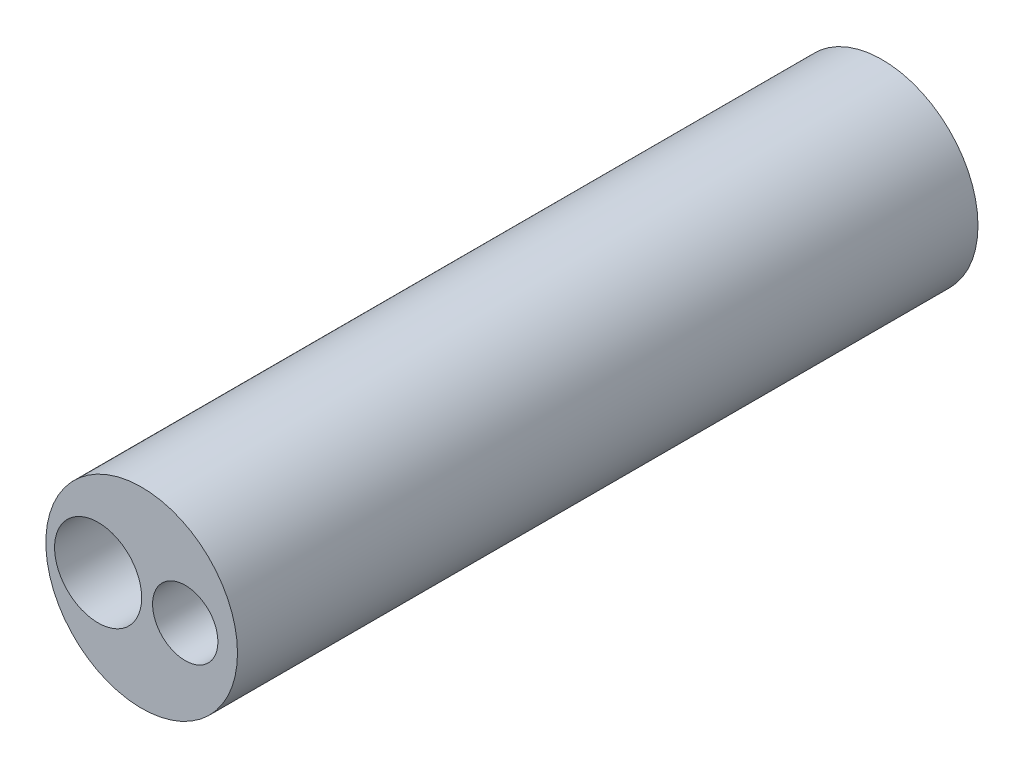
SolidWorks part; units mm, degrees
ref_plane "Front Plane" through (0, 0, 0) normal (0, 0, 1) x (1, 0, 0)
ref_plane "Top Plane" through (0, 0, 0) normal (0, 1, 0) x (1, 0, 0)
ref_plane "Right Plane" through (0, 0, 0) normal (1, 0, 0) x (0, 0, -1)
sketch "Sketch1" plane through (0, 0, 0) normal (0, 0, 1) x (1, 0, 0)
  circle A0 centre (0, 0) radius 5.08
  circle A1 centre (0, 0) radius 5.588
  dimension "D1" = 11.176
  dimension "D2" = 10.16
extrude "Boss-Extrude1" add sketch "Sketch1" along normal blind 35.56
sketch "Sketch2" plane through (0, 0, 35.56) normal (0, 0, 1) x (1, 0, 0)
  circle A0 centre (0, 0) radius 5.588
  circle A1 centre (2.54, 0) radius 1.905
  dimension "D1" = 3.81
  dimension "D2" = 11.176
  dimension "D3" = 2.54
extrude "Boss-Extrude2" add sketch "Sketch2" along normal blind 7.62
sketch "Sketch3" plane through (0, 0, 43.18) normal (0, 0, 1) x (1, 0, 0)
  circle A0 centre (-2.54, 0) radius 2.54
  dimension "D1" = 5.08
  dimension "D2" = 2.54
extrude "Cut-Extrude1" cut sketch "Sketch3" against normal blind 33.02
